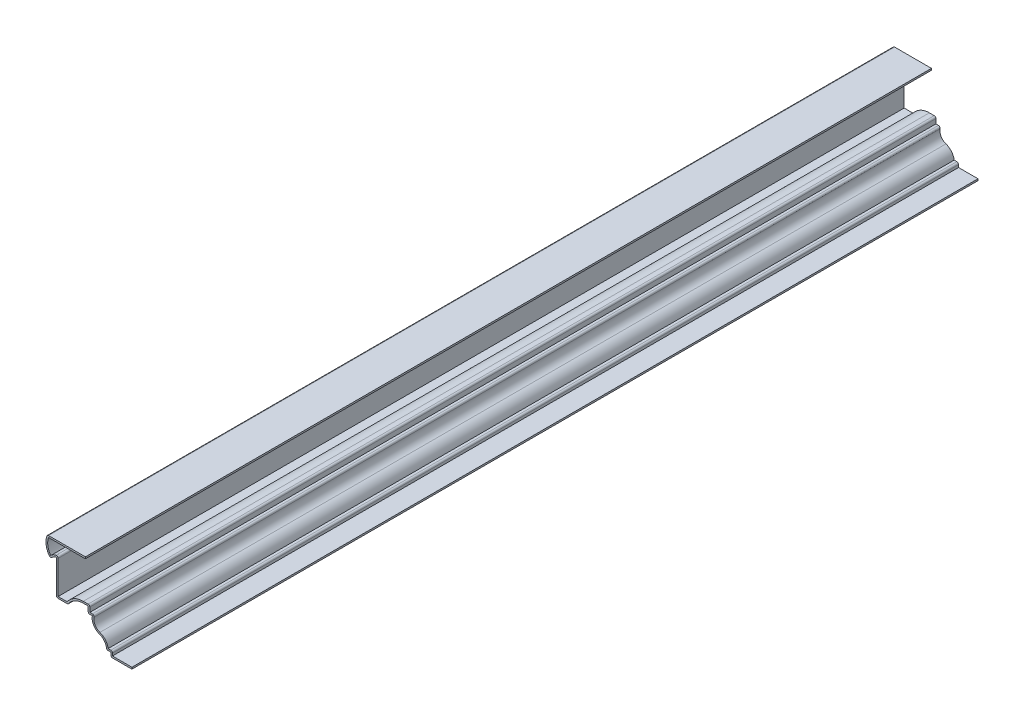
SolidWorks part; units mm, degrees
ref_plane "Front Plane" through (0, 0, 0) normal (0, 0, 1) x (1, 0, 0)
ref_plane "Top Plane" through (0, 0, 0) normal (0, 1, 0) x (1, 0, 0)
ref_plane "Right Plane" through (0, 0, 0) normal (1, 0, 0) x (0, 0, -1)
sketch "Sketch1" plane through (0, 0, 0) normal (0, 0, 1) x (1, 0, 0)
  line L0 (0, 0) -> (-15.875, 0)
  line L1 (-15.875, 0) -> (-15.875, 3.175)
  line L2 (-15.875, 3.175) -> (-19.05, 3.175)
  line L3 (-29.6854, 19.8437) -> (-32.8604, 19.8437)
  line L4 (-32.8604, 19.8437) -> (-32.8604, 24.6062)
  line L5 (-32.8604, 24.6062) -> (-36.494, 24.6062)
  line L6 (-47.9417, 18.2562) -> (-56.6729, 18.2562)
  line L7 (-56.6729, 18.2562) -> (-56.6729, 44.351)
  line L8 (-63.5, 55.5625) -> (-34.925, 55.5625)
  arc A0 (-19.05, 3.175) -> (-24.4518, 10.6966) centre (-26.9875, 3.175) ccw
  arc A1 (-24.4518, 10.6966) -> (-29.6854, 19.8437) centre (-21.9162, 18.2182) cw
  arc A2 (-36.494, 24.6062) -> (-47.9417, 18.2562) centre (-36.494, 11.1125) ccw
  arc A3 (-56.6729, 44.351) -> (-60.8766, 41.275) centre (-55.7519, 38.682) ccw
  arc A4 (-60.8766, 41.275) -> (-63.5, 55.5625) centre (-51.0031, 50.4725) cw
  point P20 (-20.3696, 17.6048)
  point P22 (-60.3087, 41.275)
  point P23 (0, 0)
  point P24 (-52.0508, 53.6792)
  point P25 (-60.5547, 41.275)
  point P26 (-60.8766, 41.275)
  point P27 (-55.7519, 44.4254)
  dimension "D7" = 7.9375
  dimension "D8" = 7.9375
  dimension "D12" = 13.4937
  dimension "D16" = 13.4937
  dimension "D19" = 56.6729
  dimension "D20" = 26.0948
  dimension "D22" = 5.7433
  dimension "D1" = 55.5625
  dimension "D2" = 63.5
  dimension "D3" = 28.575
  dimension "D4" = 15.875
  dimension "D5" = 3.175
  dimension "D6" = 3.175
  dimension "D9" = 3.175
  dimension "D10" = 4.7625
  dimension "D11" = 16.6687
  dimension "D13" = 15.0812
  dimension "D14" = 8.7312
  dimension "D15" = 15.0812
  dimension "D17" = 14.2875
  dimension "D18" = 23.0188
  dimension "D21" = 4.2037
extrude "Extrude-Thin1" add sketch "Sketch1" against normal blind 635 thin
fillet "Fillet1" radius 1.27 11 edges at (-15.875, 0, -317.5) (-14.605, 4.445, -317.5) (-19.05, 3.175, -317.5) (-27.9221, 21.1137, -317.5) (-32.8604, 19.8437, -317.5) (-31.5904, 25.8762, -317.5) (-47.9417, 18.2562, -317.5) (-56.6729, 18.2562, -317.5) (-55.4029, 45.6867, -317.5) (-60.8766, 41.275, -317.5) (-63.5, 55.5625, -317.5)
